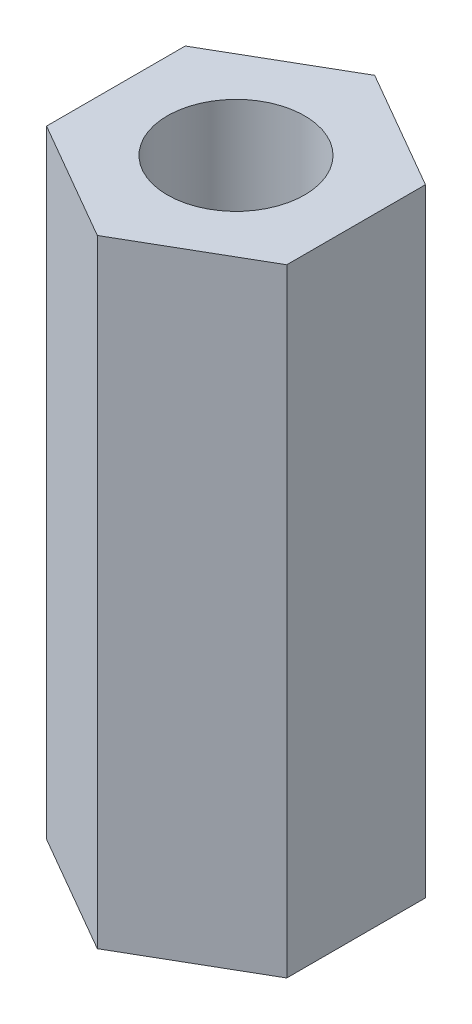
SolidWorks part; units mm, degrees
ref_plane "Piano frontale" through (0, 0, 0) normal (0, 0, 1) x (1, 0, 0)
ref_plane "Piano superiore" through (0, 0, 0) normal (0, 1, 0) x (1, 0, 0)
ref_plane "Piano destro" through (0, 0, 0) normal (1, 0, 0) x (0, 0, -1)
sketch "Sketch1" plane through (0, 0, 0) normal (0, 1, 0) x (1, 0, 0)
  line L1 (-34.9518, 18.2485) -> (-38.4518, 16.2278)
  line L2 (-38.4518, 16.2278) -> (-38.4518, 12.1863)
  line L3 (-38.4518, 12.1863) -> (-34.9518, 10.1656)
  line L4 (-34.9518, 10.1656) -> (-31.4518, 12.1863)
  line L5 (-31.4518, 12.1863) -> (-31.4518, 16.2278)
  line L6 (-31.4518, 16.2278) -> (-34.9518, 18.2485)
  circle A0 centre (-34.9518, 14.207) radius 3.5 construction
  circle A1 centre (-34.9518, 14.207) radius 2
  dimension "D1" = 4
  dimension "D2" = 7
extrude "Boss-Extrude1" add sketch "Sketch1" along normal blind 18
